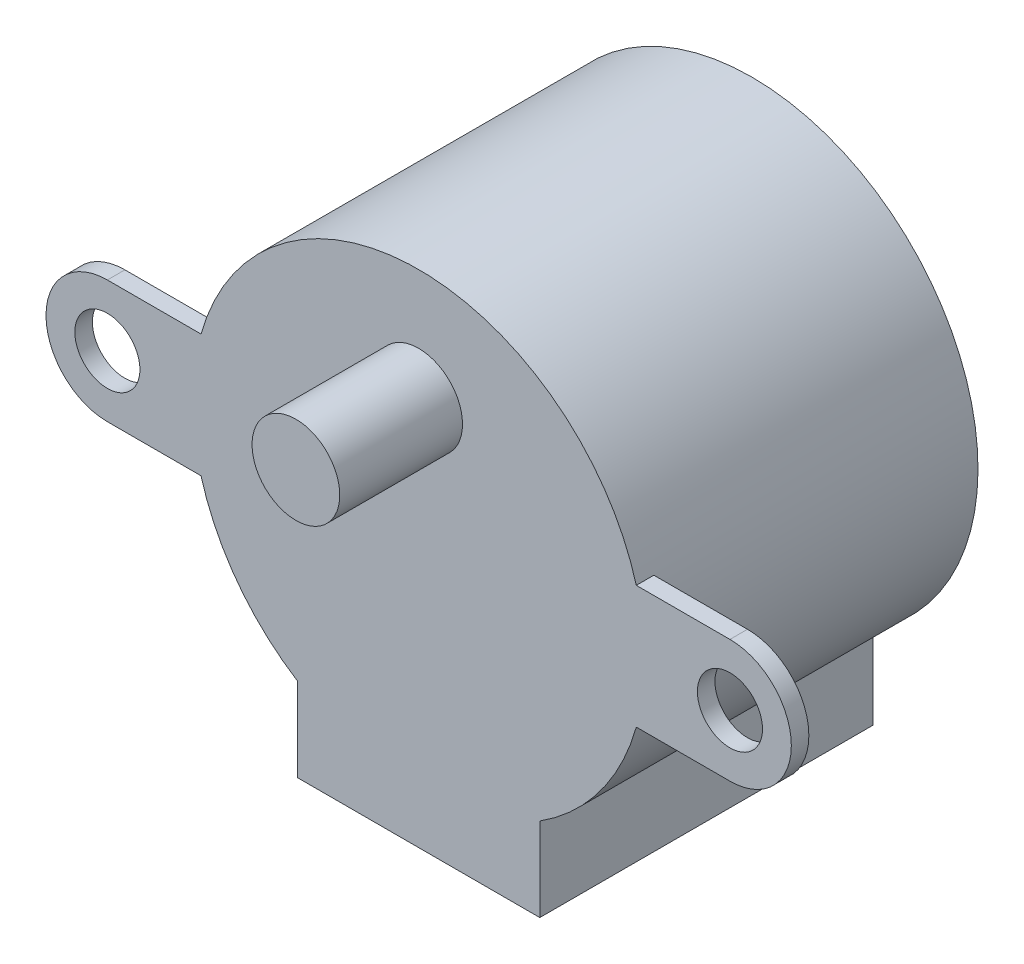
SolidWorks part; units mm, degrees
ref_plane "Plano frontal" through (0, 0, 0) normal (0, 0, 1) x (1, 0, 0)
ref_plane "Plano superior" through (0, 0, 0) normal (0, 1, 0) x (1, 0, 0)
ref_plane "Plano direito" through (0, 0, 0) normal (1, 0, 0) x (0, 0, -1)
sketch "Esboço1" plane through (0, 0, 0) normal (0, 0, 1) x (1, 0, 0)
  line L0 (17.75, 0) -> (-17.75, 0) construction
  line L1 (17.75, 3.5) -> (12.4107, 3.5)
  line L2 (-6.9079, -12.8947) -> (-6.9079, -10.8883)
  line L3 (12.4107, -3.5) -> (17.75, -3.5)
  line L4 (6.9079, -12.8947) -> (6.9079, -15.6579)
  line L5 (6.9079, -15.6579) -> (-6.9079, -15.6579)
  line L6 (6.9079, -12.8947) -> (6.9079, -10.8883)
  line L7 (-6.9079, -12.8947) -> (-6.9079, -15.6579)
  line L8 (-12.4107, -3.5) -> (-17.75, -3.5)
  line L9 (-17.75, 3.5) -> (-12.4107, 3.5)
  arc A0 (12.4107, 3.5) -> (-12.4107, 3.5) centre (0, 0) ccw
  arc A1 (17.75, -3.5) -> (17.75, 3.5) centre (17.75, 0) ccw
  circle A2 centre (17.75, 0) radius 1.8553
  arc A3 (6.9079, -10.8883) -> (12.4107, -3.5) centre (0, 0) ccw
  circle A4 centre (-17.75, 0) radius 1.8553
  arc A5 (-17.75, -3.5) -> (-17.75, 3.5) centre (-17.75, 0) cw
  arc A6 (-12.4107, -3.5) -> (-6.9079, -10.8883) centre (0, 0) ccw
  point P3 (17.732, 0)
  point P4 (0, 0)
  point P16 (0, -15.6579)
  point P18 (-6.9079, -14.2763)
  point P25 (0, 0)
  dimension "D1" = 35.5
  dimension "D2" = 3.5
extrude "Ressalto-extrusão1" add sketch "Esboço1" along normal blind 19
sketch "Esboço2" plane through (0, 0, 0) normal (0, 0, -1) x (-1, 0, 0)
  line L1 (12.4107, 3.5) -> (23.807, 3.5)
  line L3 (12.4107, -3.5) -> (23.807, -3.5)
  line L4 (23.807, 3.5) -> (23.807, -3.5)
  line L5 (-12.4107, 3.5) -> (-24.7605, 3.5)
  line L7 (-12.4107, -3.5) -> (-24.7605, -3.5)
  line L8 (-24.7605, 3.5) -> (-24.7605, -3.5)
  arc A0 (12.4107, -3.5) -> (12.4107, 3.5) centre (0, 0) ccw
  arc A1 (-12.4107, 3.5) -> (-12.4107, -3.5) centre (0, 0) ccw
extrude "Corte-extrusão1" cut sketch "Esboço2" against normal blind 18
sketch "Esboço3" plane through (0, 0, 19) normal (0, 0, 1) x (1, 0, 0)
  line L0 (-12.4107, 3.5) -> (12.4107, 3.5) construction
  line L1 (0, 3.5) -> (0, 6.5) construction
  circle A0 centre (0, 6.5) radius 2.5
extrude "Ressalto-extrusão2" add sketch "Esboço3" along normal blind 7
